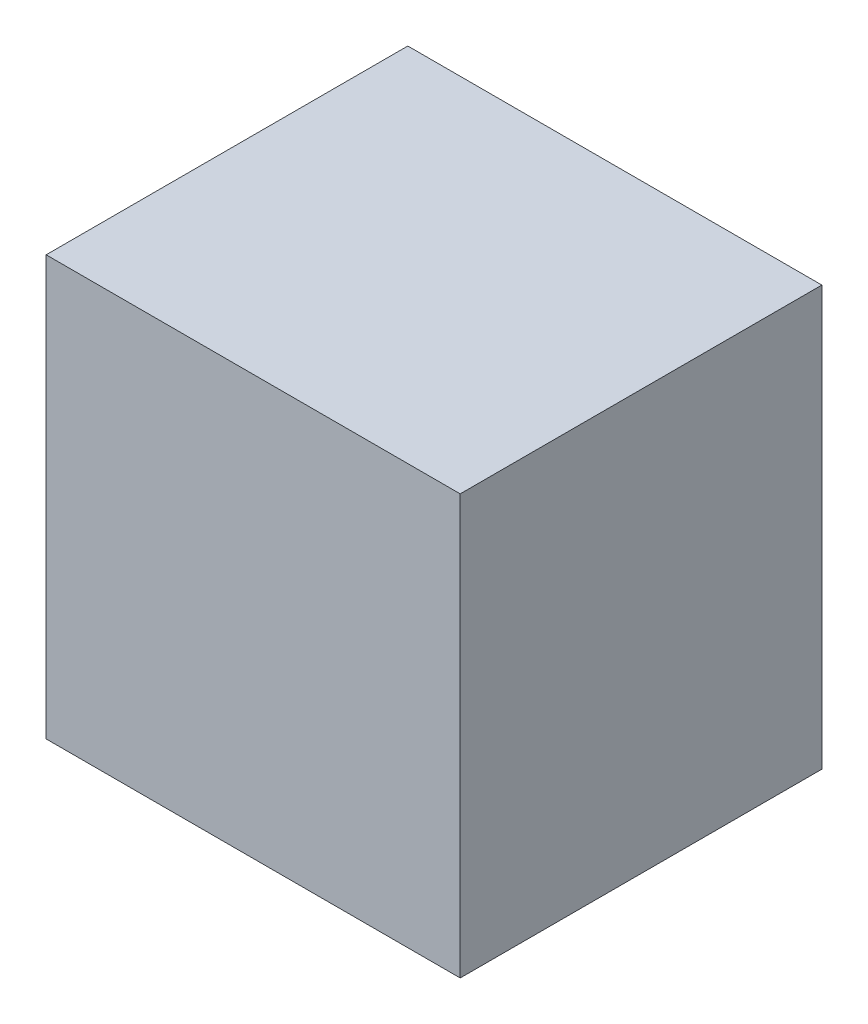
SolidWorks part; units mm, degrees
material "PEI"
ref_plane "Front Plane" through (0, 0, 0) normal (0, 0, 1) x (1, 0, 0)
ref_plane "Top Plane" through (0, 0, 0) normal (0, 1, 0) x (1, 0, 0)
ref_plane "Right Plane" through (0, 0, 0) normal (1, 0, 0) x (0, 0, -1)
sketch "Sketch1" plane through (0, 0, 0) normal (0, 1, 0) x (1, 0, 0)
  line L1 (3.95, -3.45) -> (-3.95, -3.45)
  line L2 (3.95, -3.45) -> (3.95, 3.45)
  line L3 (3.95, 3.45) -> (-3.95, 3.45)
  line L4 (-3.95, -3.45) -> (-3.95, 3.45)
  line L5 (3.95, -3.45) -> (-3.95, 3.45) construction
  line L6 (3.95, 3.45) -> (-3.95, -3.45) construction
  point P0 (0, 0)
  dimension "D1" = 6.9
  dimension "D2" = 7.9
extrude "Boss-Extrude1" add sketch "Sketch1" along normal blind 8
